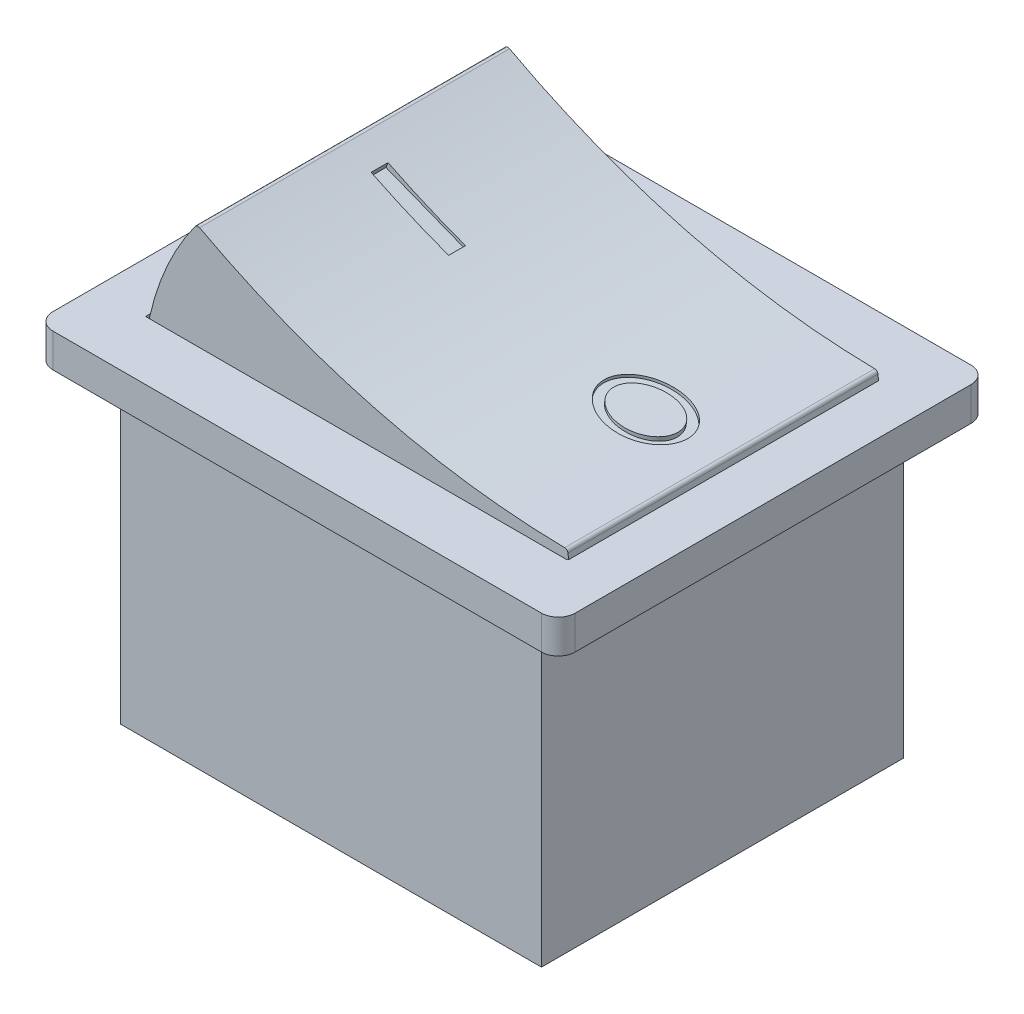
SolidWorks part; units mm, degrees
ref_plane "Alzado" through (0, 0, 0) normal (0, 0, 1) x (1, 0, 0)
ref_plane "Planta" through (0, 0, 0) normal (0, 1, 0) x (1, 0, 0)
ref_plane "Vista lateral" through (0, 0, 0) normal (1, 0, 0) x (0, 0, -1)
sketch "Croquis1" plane through (0, 0, 0) normal (0, 1, 0) x (1, 0, 0)
  line L0 (-12.5, 0) -> (12.5, 0) construction
  line L1 (-15.5, 12.75) -> (15.5, 12.75)
  line L2 (-15.5, 12.75) -> (-15.5, -12.75)
  line L3 (-15.5, -12.75) -> (15.5, -12.75)
  line L4 (15.5, 12.75) -> (15.5, -12.75)
  line L5 (-15.5, 12.75) -> (15.5, -12.75) construction
  line L6 (-15.5, -12.75) -> (15.5, 12.75) construction
  line L7 (-12.5, 9.25) -> (12.5, 9.25)
  line L8 (-12.5, 9.25) -> (-12.5, -9.25)
  line L9 (-12.5, -9.25) -> (12.5, -9.25)
  line L10 (12.5, 9.25) -> (12.5, -9.25)
  point P0 (0, 0)
  dimension "D1" = 31
  dimension "D2" = 25.5
  dimension "D3" = 25
  dimension "D4" = 18.5
extrude "Saliente-Extruir1" add sketch "Croquis1" along normal blind 2
fillet "Redondeo1" radius 1 4 edges at (-15.5, 1, -12.75) (-15.5, 1, 12.75) (15.5, 1, -12.75) (15.5, 1, 12.75)
sketch "Croquis2" plane through (0, 0, 0) normal (0, -1, 0) x (1, 0, 0)
  line L1 (-12.5, 10.75) -> (12.5, 10.75)
  line L2 (-12.5, 10.75) -> (-12.5, -10.75)
  line L3 (-12.5, -10.75) -> (12.5, -10.75)
  line L4 (12.5, 10.75) -> (12.5, -10.75)
  line L5 (-12.5, 10.75) -> (12.5, -10.75) construction
  line L6 (-12.5, -10.75) -> (12.5, 10.75) construction
  point P0 (0, 0)
  dimension "D1" = 25
  dimension "D2" = 21.5
extrude "Saliente-Extruir5" add sketch "Croquis2" along normal blind 18.2 and the other way blind 1
sketch "Croquis3" plane through (0, 0, 0) normal (0, 0, 1) x (1, 0, 0)
  line L0 (12.5, 0) -> (13.5, 0)
  line L1 (-14.5, 0) -> (14.5, 0) construction
  line L2 (13.5, 0) -> (13.5, -1)
  line L3 (12.5, 0) -> (12.5, -2)
  line L4 (12.5, 0) -> (12.5, -18.2) construction
  line L5 (0, 0) -> (0, -20.7642) construction
  line L6 (-12.5, 0) -> (-12.5, -2)
  line L7 (-13.5, 0) -> (-13.5, -1)
  line L8 (-12.5, 0) -> (-13.5, 0)
  arc A0 (12.5, -2) -> (13.5, -1) centre (12.5, -1) ccw
  arc A1 (-12.5, -2) -> (-13.5, -1) centre (-12.5, -1) cw
extrude "Saliente-Extruir6" add sketch "Croquis3" along normal mid plane 21.5
sketch "Croquis4" plane through (0, 0, 0) normal (0, 0, 1) x (1, 0, 0)
  line L0 (0, 0) -> (0, 1) construction
  line L1 (-14.5, 0) -> (14.5, 0) construction
  line L2 (-12.5, 1) -> (12.5, 1) construction
  line L3 (-12.5, 1) -> (-12.5, 8.2) construction
  line L4 (12.5, 1) -> (12.5, 2) construction
  line L5 (-12.5, 8.2) -> (-9.5, 8.2) construction
  line L6 (12.5, 2) -> (12.5, 2.5) construction
  line L7 (1.1526, 4.0093) -> (-1.3065, -5.4821) construction
  line L8 (12.5, 1) -> (13.5, 1) construction
  arc A0 (-9.3474, 8.1178) -> (12.3267, 2.5022) centre (13.018, 49.8053) ccw
  arc A1 (-9.6036, 8.0592) -> (-12.5, 1) centre (3.3834, -1.3931) ccw
  arc A2 (12.5222, 2.3266) -> (12.6295, 1) centre (-3.4208, 0.3698) cw
  arc A3 (12.5222, 2.3266) -> (12.3267, 2.5022) centre (12.3237, 2.3022) ccw
  arc A4 (-9.3474, 8.1178) -> (-9.6036, 8.0592) centre (-9.4419, 7.9415) ccw
  arc A5 (-12.5, 1) -> (12.6295, 1) centre (0.0648, 31.8354) ccw
  point P7 (0, 1)
  dimension "D1" = 0.2
extrude "Saliente-Extruir7" add sketch "Croquis4" along normal mid plane 18.4
ref_plane "Plano1" through (1.5135, 3.8681, 0) normal (-0.3644, -0.9313, 0) x (-0.9313, 0.3644, 0)
sketch "Croquis7" plane through (1.5135, 3.8681, 0) normal (-0.3644, -0.9313, 0) x (-0.9313, 0.3644, 0)
  line L0 (10, 0) -> (-10, 0) construction
  line L1 (10, 0.5) -> (10, -0.5)
  line L2 (10, 0.5) -> (5, 0.5)
  line L3 (10, -0.5) -> (5, -0.5)
  line L4 (5, 0.5) -> (5, -0.5)
  line L6 (-7.5, -1.1043) -> (-7.5, 0) construction
  ellipse E0 centre (-7.5, 0) end of major axis (-10, 0) minor radius 1.9899
  ellipse E1 centre (-7.5, 0) end of major axis (-9.4192, 0) minor radius 1.507
  point P4 (0, 0)
  point P10 (10, 0)
extrude "Cortar-Extruir2" cut sketch "Croquis7" against normal mid plane 1
ref_plane "Plano2" through (0.5517, 4.0904, 0) normal (-0.1337, -0.991, 0) x (-0.991, 0.1337, 0)
sketch "Croquis8" plane through (0.5517, 4.0904, 0) normal (-0.1337, -0.991, 0) x (-0.991, 0.1337, 0)
  line L0 (10, 0) -> (-10, 0) construction
  line L1 (10, 0.5) -> (10, -0.5)
  line L2 (10, 0.5) -> (5, 0.5)
  line L3 (10, -0.5) -> (5, -0.5)
  line L4 (5, 0.5) -> (5, -0.5)
  line L5 (-7.5, -1.1043) -> (-7.5, 0) construction
  ellipse E0 centre (-7.5, 0) end of major axis (-10, 0) minor radius 1.9899
  ellipse E1 centre (-7.5, 0) end of major axis (-9.4192, 0) minor radius 1.507
  point P3 (0, 0)
  point P9 (10, 0)
extrude "Cortar-Extruir3" cut sketch "Croquis8" against normal mid plane 1
